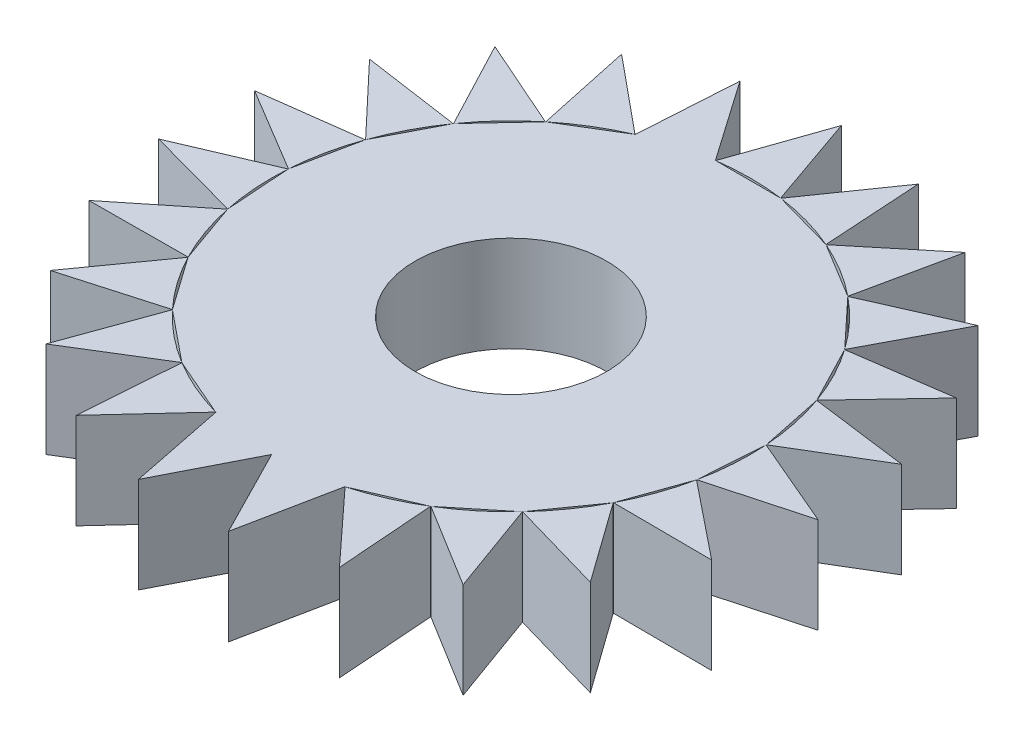
SolidWorks part; units mm, degrees
material "1023 Carbon Steel Sheet (SS)"
ref_plane "Front" through (0, 0, 0) normal (0, 0, 1) x (1, 0, 0)
ref_plane "Top" through (0, 0, 0) normal (0, 1, 0) x (1, 0, 0)
ref_plane "Right" through (0, 0, 0) normal (1, 0, 0) x (0, 0, -1)
sketch "Sketch1" plane through (0, 0, 0) normal (0, 1, 0) x (1, 0, 0)
  line L0 (0, 5) -> (0, 6.9001)
  line L1 (0, -55) -> (0, 55) construction
  line L2 (0, 6.9001) -> (-0.6783, 4.9538)
  line L3 (0, 6.9001) -> (0.6783, 4.9538)
  line L4 (0.6783, 4.9538) -> (-0.6783, 4.9538)
  line L5 (1.8616, 6.6442) -> (1.9897, 4.5871)
  line L6 (1.9897, 4.5871) -> (0.6833, 4.9531)
  line L7 (1.8616, 6.6442) -> (0.6833, 4.9531)
  line L8 (3.5852, 5.8955) -> (3.1535, 3.8801)
  line L9 (3.1535, 3.8801) -> (1.9943, 4.5851)
  line L10 (3.5852, 5.8955) -> (1.9943, 4.5851)
  line L11 (5.0428, 4.7097) -> (4.0834, 2.8855)
  line L12 (4.0834, 2.8855) -> (3.1574, 3.877)
  line L13 (5.0428, 4.7097) -> (3.1574, 3.877)
  line L14 (6.1265, 3.1745) -> (4.7105, 1.6768)
  line L15 (4.7105, 1.6768) -> (4.0863, 2.8813)
  line L16 (6.1265, 3.1745) -> (4.0863, 2.8813)
  line L17 (6.7557, 1.4039) -> (4.9882, 0.3437)
  line L18 (4.9882, 0.3437) -> (4.7121, 1.672)
  line L19 (6.7557, 1.4039) -> (4.7121, 1.672)
  line L20 (6.884, -0.4709) -> (4.8959, -1.0148)
  line L21 (4.8959, -1.0148) -> (4.9885, 0.3387)
  line L22 (6.884, -0.4709) -> (4.9885, 0.3387)
  line L23 (6.5017, -2.3107) -> (4.4406, -2.2981)
  line L24 (4.4406, -2.2981) -> (4.8949, -1.0197)
  line L25 (6.5017, -2.3107) -> (4.8949, -1.0197)
  line L26 (5.6371, -3.9791) -> (3.6559, -3.4109)
  line L27 (3.6559, -3.4109) -> (4.4383, -2.3026)
  line L28 (5.6371, -3.9791) -> (4.4383, -2.3026)
  line L29 (4.3545, -5.3525) -> (2.6001, -4.2708)
  line L30 (2.6001, -4.2708) -> (3.6525, -3.4146)
  line L31 (4.3545, -5.3525) -> (3.6525, -3.4146)
  line L32 (2.749, -6.3288) -> (1.3514, -4.8139)
  line L33 (1.3514, -4.8139) -> (2.5958, -4.2734)
  line L34 (2.749, -6.3288) -> (2.5958, -4.2734)
  line L35 (0.9396, -6.8358) -> (0.0025, -5)
  line L36 (0.0025, -5) -> (1.3466, -4.8153)
  line L37 (0.9396, -6.8358) -> (1.3466, -4.8153)
  line L38 (-0.9396, -6.8358) -> (-1.3466, -4.8153)
  line L39 (-1.3466, -4.8153) -> (-0.0025, -5)
  line L40 (-0.9396, -6.8358) -> (-0.0025, -5)
  line L41 (-2.749, -6.3288) -> (-2.5958, -4.2734)
  line L42 (-2.5958, -4.2734) -> (-1.3514, -4.8139)
  line L43 (-2.749, -6.3288) -> (-1.3514, -4.8139)
  line L44 (-4.3545, -5.3525) -> (-3.6525, -3.4146)
  line L45 (-3.6525, -3.4146) -> (-2.6001, -4.2708)
  line L46 (-4.3545, -5.3525) -> (-2.6001, -4.2708)
  line L47 (-5.6371, -3.9791) -> (-4.4383, -2.3026)
  line L48 (-4.4383, -2.3026) -> (-3.6559, -3.4109)
  line L49 (-5.6371, -3.9791) -> (-3.6559, -3.4109)
  line L50 (-6.5017, -2.3107) -> (-4.8949, -1.0197)
  line L51 (-4.8949, -1.0197) -> (-4.4406, -2.2981)
  line L52 (-6.5017, -2.3107) -> (-4.4406, -2.2981)
  line L53 (-6.884, -0.4709) -> (-4.9885, 0.3387)
  line L54 (-4.9885, 0.3387) -> (-4.8959, -1.0148)
  line L55 (-6.884, -0.4709) -> (-4.8959, -1.0148)
  line L56 (-6.7557, 1.4039) -> (-4.7121, 1.672)
  line L57 (-4.7121, 1.672) -> (-4.9882, 0.3437)
  line L58 (-6.7557, 1.4039) -> (-4.9882, 0.3437)
  line L59 (-6.1265, 3.1745) -> (-4.0863, 2.8813)
  line L60 (-4.0863, 2.8813) -> (-4.7105, 1.6768)
  line L61 (-6.1265, 3.1745) -> (-4.7105, 1.6768)
  line L62 (-5.0428, 4.7097) -> (-3.1574, 3.877)
  line L63 (-3.1574, 3.877) -> (-4.0834, 2.8855)
  line L64 (-5.0428, 4.7097) -> (-4.0834, 2.8855)
  line L65 (-3.5852, 5.8955) -> (-1.9943, 4.5851)
  line L66 (-1.9943, 4.5851) -> (-3.1535, 3.8801)
  line L67 (-3.5852, 5.8955) -> (-3.1535, 3.8801)
  line L68 (-1.8616, 6.6442) -> (-0.6833, 4.9531)
  line L69 (-0.6833, 4.9531) -> (-1.9897, 4.5871)
  line L70 (-1.8616, 6.6442) -> (-1.9897, 4.5871)
  line L71 (-55, 0) -> (55, 0) construction
  circle A0 centre (0, 0) radius 2
  circle A1 centre (0, 0) radius 5
  point P79 (0, 0)
  dimension "D1" = 4
  dimension "D2" = 10
  dimension "D3" = 1.9001
  dimension "D4" = 1.3567
  dimension "D6" = 4.7097
  dimension "D7" = 5.0428
  dimension "D5" = 23
extrude "Boss-Extrude1" add sketch "Sketch1" along normal blind 2 contours L36 A1 L33 L30 L27 L24 L21 L18 L15 L12 L9 L6 L4 L69 L66 L63 L60 L57 L54 L51 L48 L45 L42 L39 A0 | A1 L59 L61 | A1 L62 L64 | A1 L65 L67 | A1 L0 L2 | A1 L3 L0 | A1 L5 L7 | A1 L8 L10 | A1 L11 L13 | A1 L14 L16 | A1 L17 L19 | A1 L20 L22 | A1 L23 L25 | A1 L26 L28 | A1 L29 L31 | A1 L32 L34 | A1 L41 L43 | A1 L44 L46 | A1 L47 L49 | A1 L50 L52 | A1 L53 L55 | A1 L56 L58
